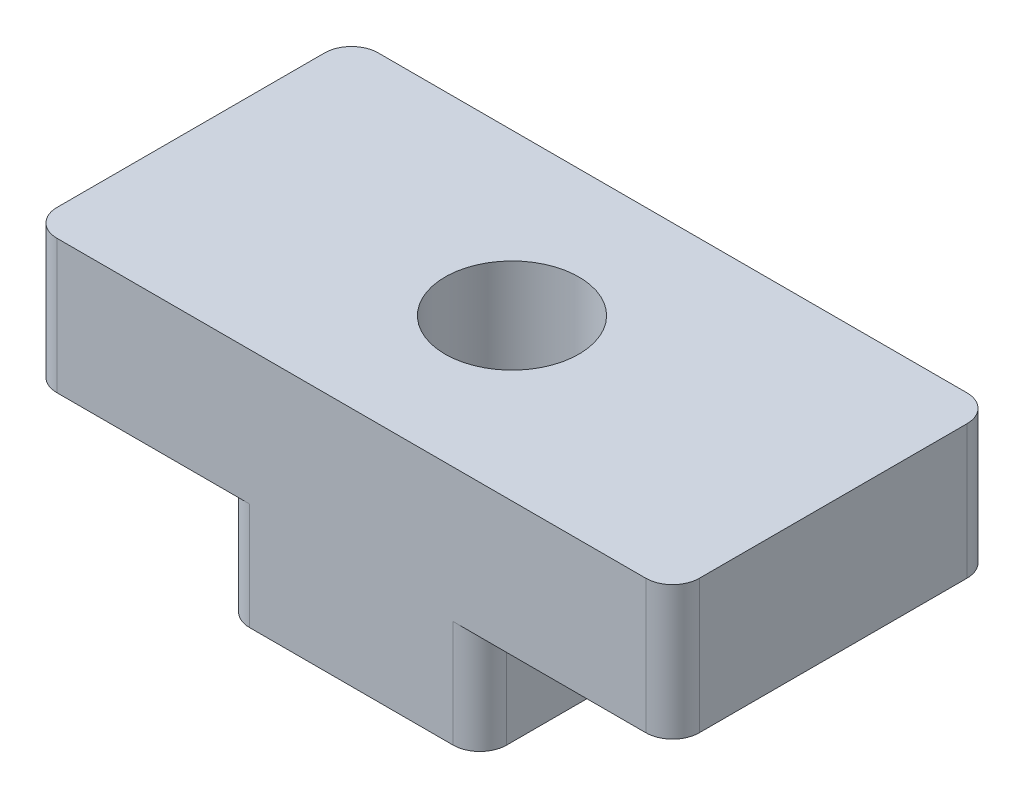
SolidWorks part; units mm, degrees
ref_plane "Plan de face" through (0, 0, 0) normal (0, 0, 1) x (1, 0, 0)
ref_plane "Plan de dessus" through (0, 0, 0) normal (0, 1, 0) x (1, 0, 0)
ref_plane "Plan de droite" through (0, 0, 0) normal (1, 0, 0) x (0, 0, -1)
sketch "Esquisse1" plane through (0, 0, 0) normal (0, 0, 1) x (1, 0, 0)
  line L0 (-6, 0) -> (-2.4, 0)
  line L1 (-2.4, -2) -> (2.4, -2)
  line L2 (-6, 0) -> (-6, 2.5)
  line L3 (-6, 2.5) -> (6, 2.5)
  line L4 (6, 0) -> (6, 2.5)
  line L5 (-6, 0) -> (6, 0) construction
  line L7 (-2.4, 0) -> (-2.4, -2)
  line L8 (6, 0) -> (2.4, 0)
  line L9 (2.4, 0) -> (2.4, -2)
  point P0 (0, 0)
  dimension "D1" = 12
  dimension "D2" = 4.8
  dimension "D3" = 2.5
  dimension "D4" = 2
extrude "Boss.-Extru.1" add sketch "Esquisse1" along normal mid plane 6
sketch "Esquisse2" plane through (0, 2.5, 0) normal (0, 1, 0) x (1, 0, 0)
  circle A0 centre (0, 0) radius 1.25
  dimension "D1" = 2.5
extrude "Enlèv. mat.-Extru.1" cut sketch "Esquisse2" against normal through all
fillet "Congé1" radius 0.5 8 edges at (-6, 1.25, -3) (-2.4, -1, -3) (2.4, -1, -3) (6, 1.25, -3) (2.4, -1, 3) (-2.4, -1, 3) (-6, 1.25, 3) (6, 1.25, 3)
